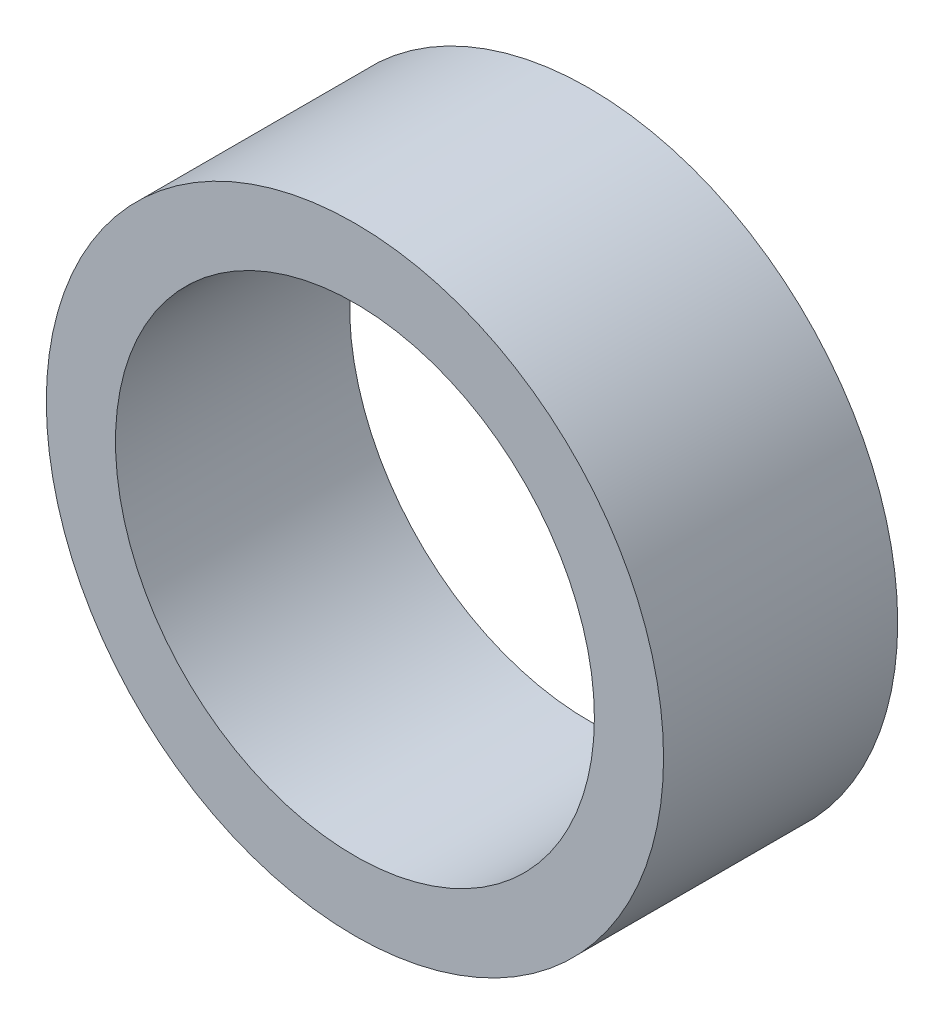
SolidWorks part; units mm, degrees
ref_plane "前视基准面" through (0, 0, 0) normal (0, 0, 1) x (1, 0, 0)
ref_plane "上视基准面" through (0, 0, 0) normal (0, 1, 0) x (1, 0, 0)
ref_plane "右视基准面" through (0, 0, 0) normal (1, 0, 0) x (0, 0, -1)
sketch "草图1" plane through (0, 0, 0) normal (0, 0, 1) x (1, 0, 0)
  circle A0 centre (0, 0) radius 22.5
  circle A1 centre (0, 0) radius 29
  dimension "D1" = 45
  dimension "D2" = 58
extrude "凸台-拉伸1" add sketch "草图1" along normal blind 22
